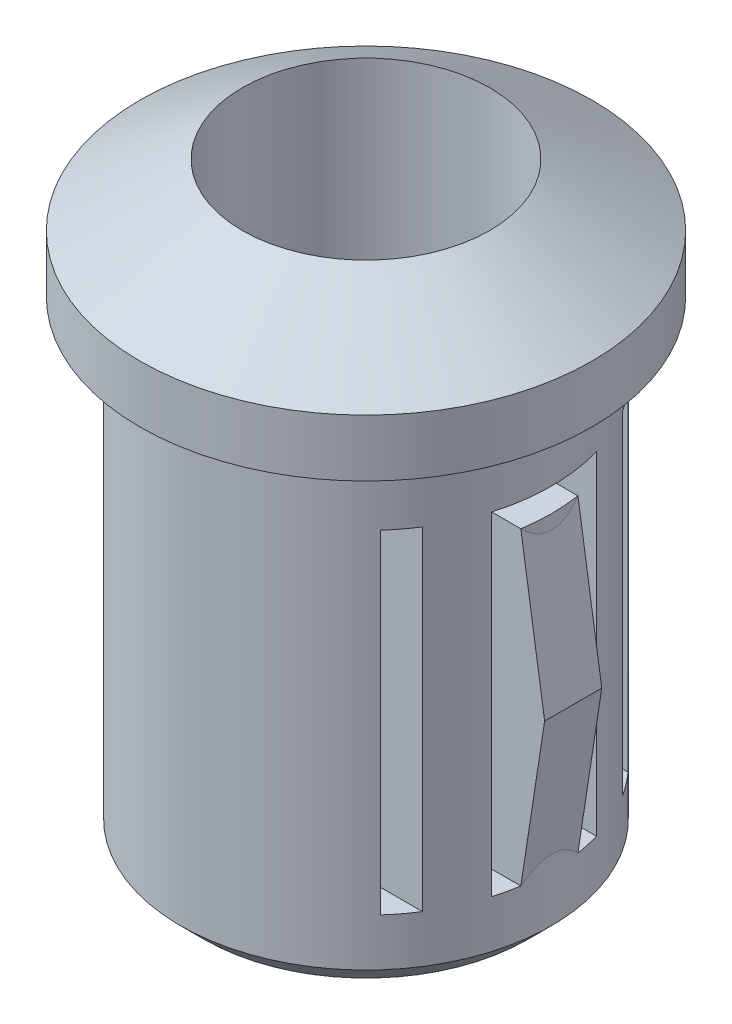
SolidWorks part; units mm, degrees
ref_plane "Front Plane" through (0, 0, 0) normal (0, 0, 1) x (1, 0, 0)
ref_plane "Top Plane" through (0, 0, 0) normal (0, 1, 0) x (1, 0, 0)
ref_plane "Right Plane" through (0, 0, 0) normal (1, 0, 0) x (0, 0, -1)
sketch "Sketch1" plane through (0, 0, 0) normal (0, 0, 1) x (1, 0, 0)
  line L0 (2.6, 0) -> (2.6, 4)
  line L1 (2.6, 4) -> (4.75, 2.7)
  line L2 (4.75, 2.7) -> (4.75, 1.5)
  line L3 (4.75, 1.5) -> (3.9, 1.5)
  line L4 (3.9, 1.5) -> (3.9, -8.5)
  line L5 (3.9, -8.5) -> (3.1, -8.5)
  line L6 (3.1, -8.5) -> (3.1, 0)
  line L7 (3.1, 0) -> (2.6, 0)
  line L8 (2.6, 0) -> (0, 0) construction
  line L9 (0, 42.244) -> (0, -30.1119) construction
  dimension "D1" = 9.5
  dimension "D2" = 5.2
  dimension "D3" = 1.2
  dimension "D4" = 10
  dimension "D5" = 0.8
  dimension "D6" = 7.8
  dimension "D7" = 2.5
  dimension "D8" = 4
revolve "Revolve1" add sketch "Sketch1" angle 360 about L9
sketch "Sketch2" plane through (0, 0, 0) normal (1, 0, 0) x (0, 0, -1)
  line L0 (0.6, -7) -> (1.1, -7)
  line L1 (-2.6, 0) -> (-2.1, 0)
  line L2 (-2.6, 0) -> (-2.6, -7)
  line L3 (-2.6, -7) -> (-2.1, -7)
  line L4 (-2.1, 0) -> (-2.1, -7)
  line L5 (2.1, 0) -> (2.6, 0)
  line L6 (2.1, 0) -> (2.1, -7)
  line L7 (2.1, -7) -> (2.6, -7)
  line L8 (2.6, 0) -> (2.6, -7)
  line L9 (-1.1, 0) -> (1.1, 0)
  line L10 (-1.1, 0) -> (-1.1, -7)
  line L11 (-1.1, -7) -> (-0.6, -7)
  line L12 (1.1, 0) -> (1.1, -7)
  line L14 (-0.6, -7) -> (-0.6, -0.5)
  line L15 (-0.6, -0.5) -> (0.6, -0.5)
  line L16 (0.6, -7) -> (0.6, -0.5)
  point P15 (0, 0)
  dimension "D1" = 7
  dimension "D2" = 0.5
  dimension "D3" = 1.2
  dimension "D4" = 0.5
  dimension "D5" = 1
  dimension "D6" = 1
extrude "Cut-Extrude1" cut sketch "Sketch2" against normal through all and the other way through all
sketch "Sketch3" plane through (0, 0, 0.6) normal (0, 0, 1) x (1, 0, 0)
  line L0 (3.8536, -0.5) -> (4.3536, -3.75)
  line L1 (4.3536, -3.75) -> (3.8536, -7)
  line L2 (3.8536, -7) -> (3.8536, -0.5)
  line L3 (4.3536, -3.75) -> (3.8536, -3.75) construction
  dimension "D1" = 0.5
extrude "Boss-Extrude1" add sketch "Sketch3" against normal up to surface (1.2 mm away) up to face at (3.4475, -3.75, -0.6)
mirror "Mirror1" about plane through (0, 0, 0) normal (1, 0, 0) of "Boss-Extrude1"
chamfer "Chamfer1" distance 0.5 angle 45 1 edges at (-3.9, -8.5, 0)
